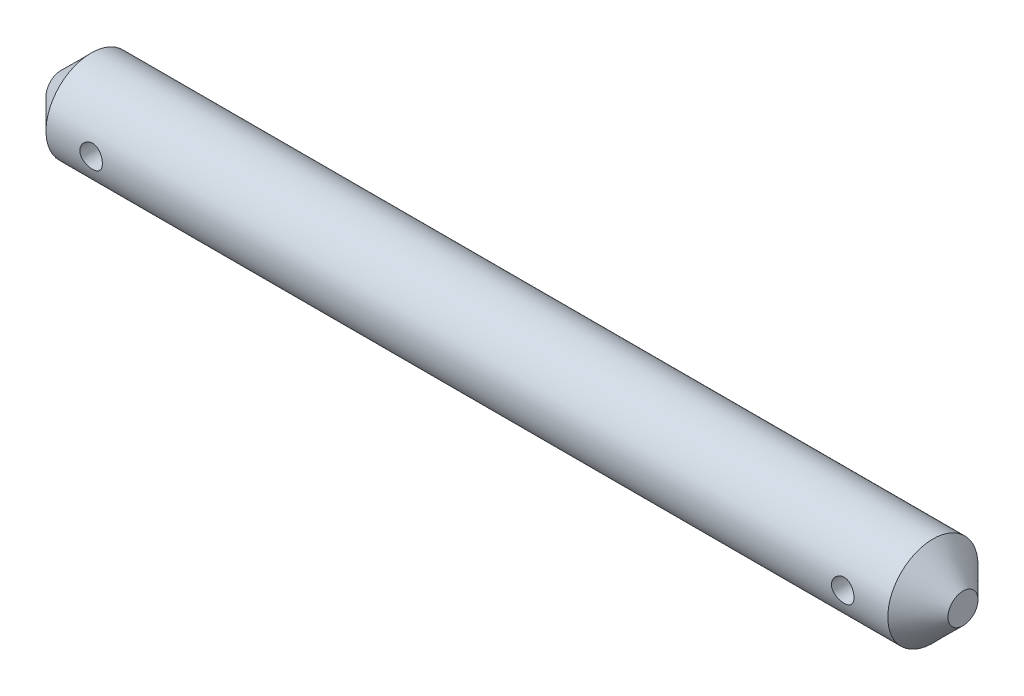
SolidWorks part; units mm, degrees
ref_plane "Спереди" through (0, 0, 0) normal (0, 0, 1) x (1, 0, 0)
ref_plane "Сверху" through (0, 0, 0) normal (0, 1, 0) x (1, 0, 0)
ref_plane "Справа" through (0, 0, 0) normal (1, 0, 0) x (0, 0, -1)
sketch "Эскиз1" plane through (0, 0, 0) normal (1, 0, 0) x (0, 0, -1)
  circle A0 centre (0, 0) radius 3
  dimension "D1" = 6
extrude "Бобышка-Вытянуть1" add sketch "Эскиз1" along normal blind 60 contours A0
chamfer "Фаска1" distance 2 angle 45 2 edges at (0, 0, -3) (60, 0, -3)
sketch "Эскиз2" plane through (0, 0, 0) normal (0, 0, 1) x (1, 0, 0)
  line L0 (0, 0) -> (60, 0) construction
  line L1 (60, -1) -> (60, 1) construction
  circle A0 centre (5, 0) radius 0.75
  circle A1 centre (55, 0) radius 0.75
  dimension "D1" = 1.5
  dimension "D2" = 5
  dimension "D3" = 50
extrude "Вырез-Вытянуть1" cut sketch "Эскиз2" against normal through all both and the other way through all
